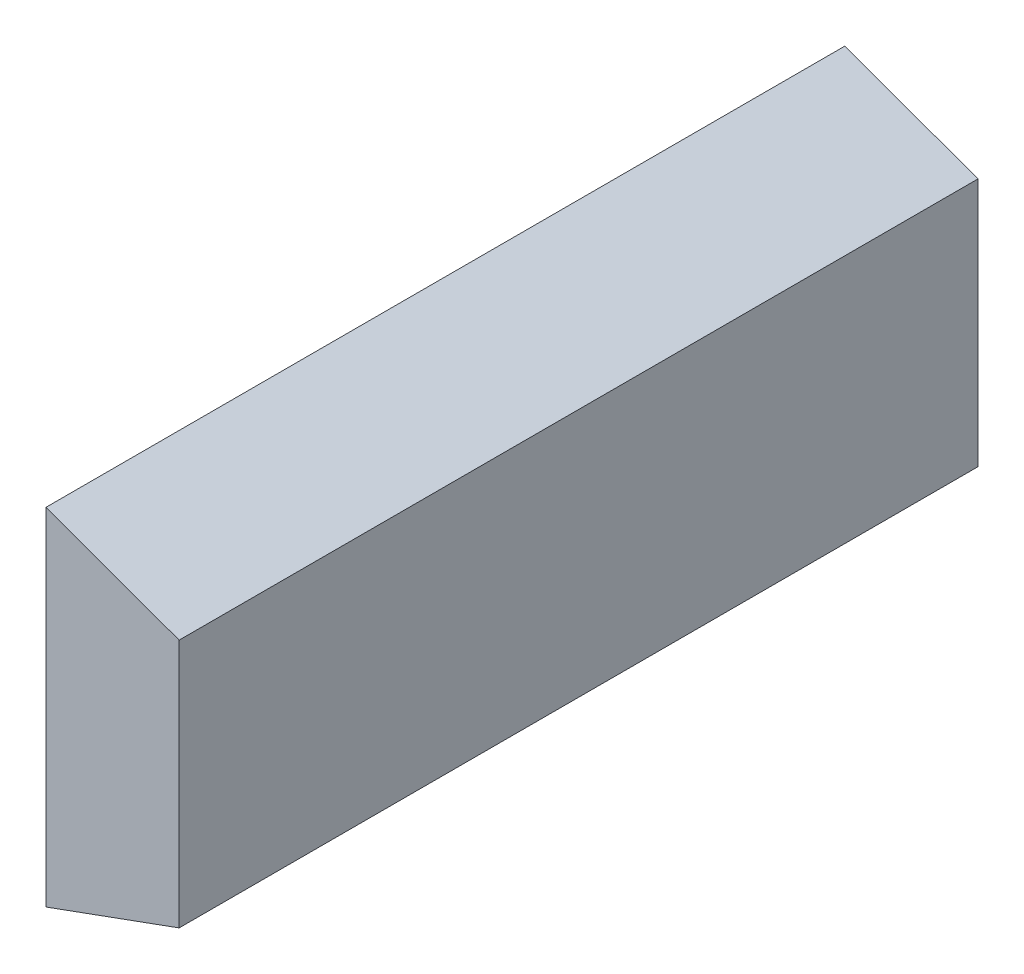
SolidWorks part; units mm, degrees
ref_plane "Front Plane" through (0, 0, 0) normal (0, 0, 1) x (1, 0, 0)
ref_plane "Top Plane" through (0, 0, 0) normal (0, 1, 0) x (1, 0, 0)
ref_plane "Right Plane" through (0, 0, 0) normal (1, 0, 0) x (0, 0, -1)
sketch "Sketch1" plane through (0, 0, 0) normal (0, 0, 1) x (1, 0, 0)
  line L0 (61.7537, -16.4049) -> (61.7537, -18.1549) construction
  line L1 (61.7537, 0) -> (61.7537, -1.4715) construction
  line L2 (61.7537, -18.1549) -> (61.7537, -24.6549)
  line L3 (61.7537, -24.6549) -> (61.7537, -26.4049) construction
  line L4 (61.7537, -18.1549) -> (64.2537, -19.0648)
  line L5 (64.2537, -19.0648) -> (64.2537, -23.745)
  line L6 (64.2537, -23.745) -> (61.7537, -24.6549)
  line L7 (61.7537, -18.1549) -> (64.2537, -18.1549) construction
  line L8 (64.2537, -18.1549) -> (64.2537, -19.0648) construction
  line L9 (61.7537, -24.6549) -> (64.2537, -24.6549) construction
  line L10 (64.2537, -24.6549) -> (64.2537, -23.745) construction
  line L12 (62.4124, -5.685) -> (62.0055, -3.6248) construction
  point P12 (62.209, -4.6549)
  dimension "D1" = 1.75
  dimension "D2" = 1.75
  dimension "D3" = 10
  dimension "D4" = 2.5
  dimension "D5" = 20
  dimension "D6" = 20
  dimension "D7" = 11.75
extrude "Boss-Extrude1" add sketch "Sketch1" against normal blind 15
